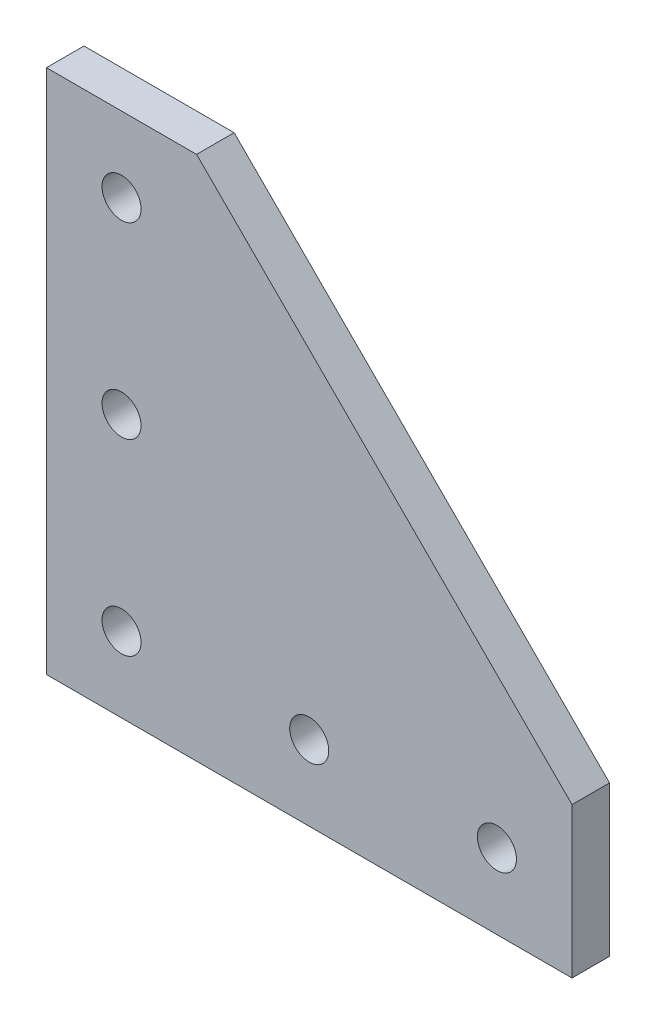
SolidWorks part; units mm, degrees
ref_plane "Front Plane" through (0, 0, 0) normal (0, 0, 1) x (1, 0, 0)
ref_plane "Top Plane" through (0, 0, 0) normal (0, 1, 0) x (1, 0, 0)
ref_plane "Right Plane" through (0, 0, 0) normal (1, 0, 0) x (0, 0, -1)
sketch "Sketch1" plane through (0, 0, 0) normal (0, 0, 1) x (1, 0, 0)
  line L0 (0, 0) -> (0, 88.9)
  line L1 (0, 88.9) -> (25.4, 88.9)
  line L2 (25.4, 88.9) -> (88.9, 25.4)
  line L3 (88.9, 25.4) -> (88.9, 0)
  line L4 (88.9, 0) -> (0, 0)
  line L5 (0, 0) -> (-0.266, -0.133)
  line L6 (12.7, 12.7) -> (12.7, 76.2) construction
  line L7 (12.7, 12.7) -> (76.2, 12.7) construction
  circle A0 centre (12.7, 12.7) radius 3.302
  circle A1 centre (12.7, 44.45) radius 3.302
  circle A2 centre (12.7, 76.2) radius 3.302
  circle A3 centre (44.45, 12.7) radius 3.302
  circle A4 centre (76.2, 12.7) radius 3.302
  dimension "D5" = 6.604
  dimension "D1" = 25.4
  dimension "D2" = 25.4
  dimension "D3" = 88.9
  dimension "D4" = 88.9
  dimension "D6" = 12.7
  dimension "D7" = 12.7
  dimension "D8" = 63.5
  dimension "D9" = 63.5
extrude "Boss-Extrude1" add sketch "Sketch1" along normal blind 6.35 contours L4 L3 L2 L1 L0 A4 A3 A2 A1 A0
